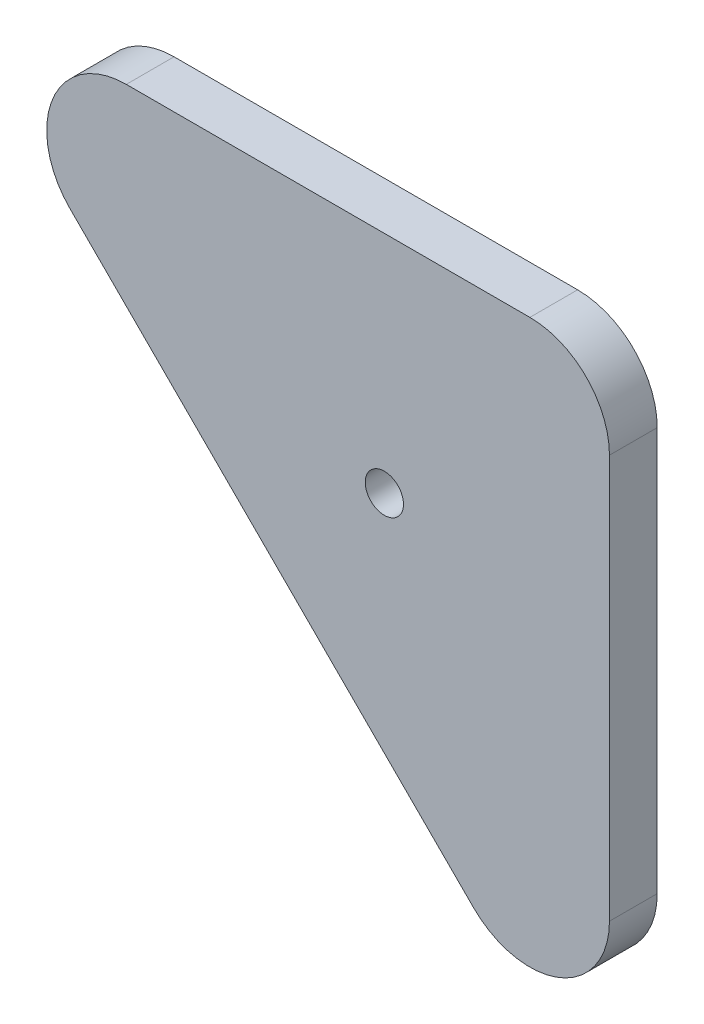
SolidWorks part; units mm, degrees
ref_plane "Front Plane" through (0, 0, 0) normal (0, 0, 1) x (1, 0, 0)
ref_plane "Top Plane" through (0, 0, 0) normal (0, 1, 0) x (1, 0, 0)
ref_plane "Right Plane" through (0, 0, 0) normal (1, 0, 0) x (0, 0, -1)
sketch "Sketch1" plane through (0, 0, 0) normal (0, 0, 1) x (1, 0, 0)
  line L0 (552.9289, 502.2183) -> (502.2183, 552.9289)
  line L1 (570, 570) -> (570, -570) construction
  line L2 (-570, 570) -> (570, 570) construction
  line L3 (509.2893, 570) -> (560, 570)
  line L4 (570, 560) -> (570, 509.2893)
  line L5 (570, 570) -> (527.5736, 527.5736) construction
  circle A0 centre (541.7157, 541.7157) radius 2.4
  arc A1 (502.2183, 552.9289) -> (509.2893, 570) centre (509.2893, 560) cw
  arc A2 (560, 570) -> (570, 560) centre (560, 560) cw
  arc A3 (552.9289, 502.2183) -> (570, 509.2893) centre (560, 509.2893) ccw
  point P13 (485.1472, 570)
  point P19 (570, 485.1472)
  dimension "D3" = 4.8
  dimension "D4" = 20
  dimension "D5" = 10
  dimension "D1" = 45
  dimension "D2" = 60
extrude "Boss-Extrude1" add sketch "Sketch1" along normal blind 6
